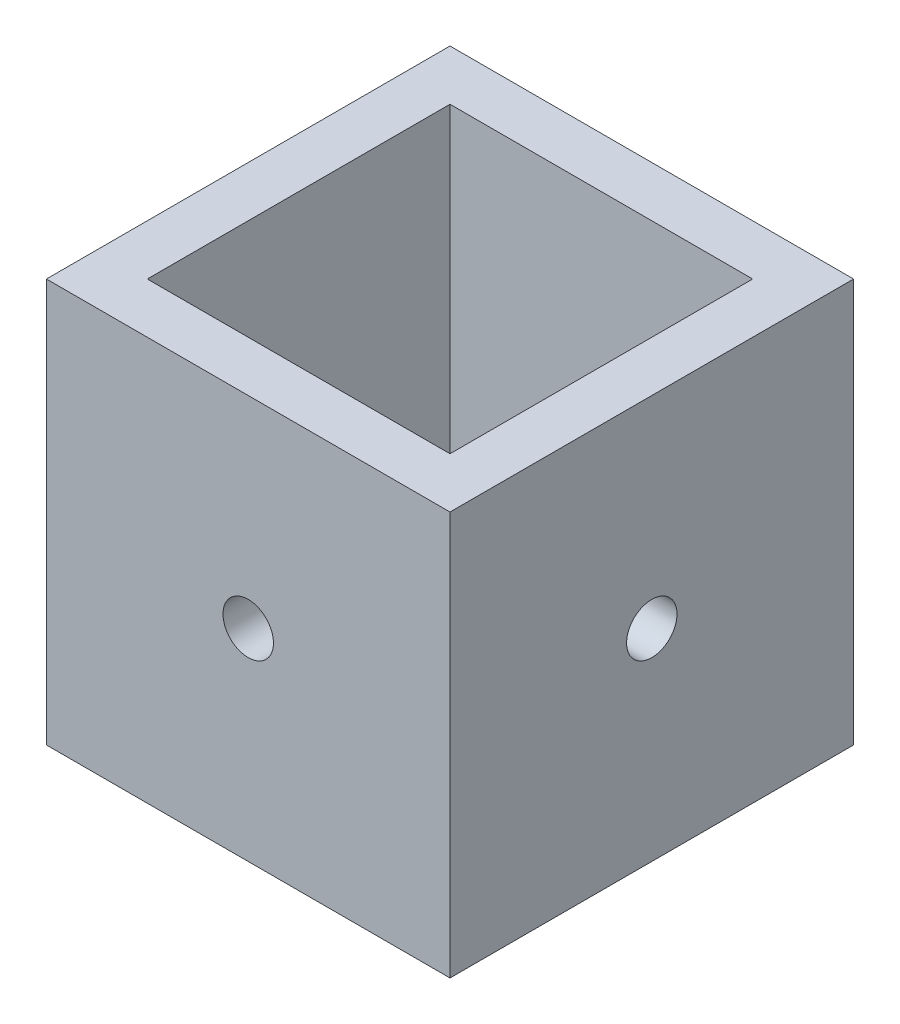
SolidWorks part; units mm, degrees
ref_plane "Front" through (0, 0, 0) normal (0, 0, 1) x (1, 0, 0)
ref_plane "Top" through (0, 0, 0) normal (0, 1, 0) x (1, 0, 0)
ref_plane "Right" through (0, 0, 0) normal (1, 0, 0) x (0, 0, -1)
sketch "스케치5" plane through (0, 0, 0) normal (0, 1, 0) x (1, 0, 0)
  line L1 (12.7, -12.7) -> (-12.7, -12.7)
  line L2 (12.7, -12.7) -> (12.7, 12.7)
  line L3 (12.7, 12.7) -> (-12.7, 12.7)
  line L4 (-12.7, -12.7) -> (-12.7, 12.7)
  line L5 (0, 12.7) -> (0, -12.7) construction
  line L6 (12.7, 0) -> (-12.7, 0) construction
  line L7 (9.525, -9.525) -> (-9.525, -9.525)
  line L8 (9.525, -9.525) -> (9.525, 9.525)
  line L9 (9.525, 9.525) -> (-9.525, 9.525)
  line L10 (-9.525, -9.525) -> (-9.525, 9.525)
  line L11 (0, 9.525) -> (0, -9.525) construction
  line L12 (9.525, 0) -> (-9.525, 0) construction
  point P0 (0, 0)
  point P4 (0, 0)
  dimension "D1" = 3.175
  dimension "D2" = 3.175
  dimension "D3" = 25.4
  dimension "D4" = 25.4
extrude "보스-돌출1" add sketch "스케치5" along normal blind 25.4
sketch "스케치6" plane through (0, 0, 12.7) normal (0, 0, 1) x (1, 0, 0)
  line L0 (-12.7, 0) -> (12.7, 0) construction
  line L1 (-12.7, 25.4) -> (-12.7, 0) construction
  circle A0 centre (0, 12.7) radius 1.5875
  dimension "D1" = 12.7
  dimension "D2" = 3.175
  dimension "D3" = 12.7
extrude "컷-돌출1" cut sketch "스케치6" against normal blind 30.48
sketch "스케치7" plane through (12.7, 0, 0) normal (1, 0, 0) x (0, 0, -1)
  line L0 (-12.7, 0) -> (12.7, 0) construction
  line L2 (-12.7, 25.4) -> (-12.7, 0) construction
  circle A0 centre (0, 12.7) radius 1.5875
  point P6 (-11.3344, 13.8992)
  dimension "D1" = 12.7
  dimension "D2" = 3.175
  dimension "D3" = 12.7
extrude "컷-돌출2" cut sketch "스케치7" against normal blind 30.48
